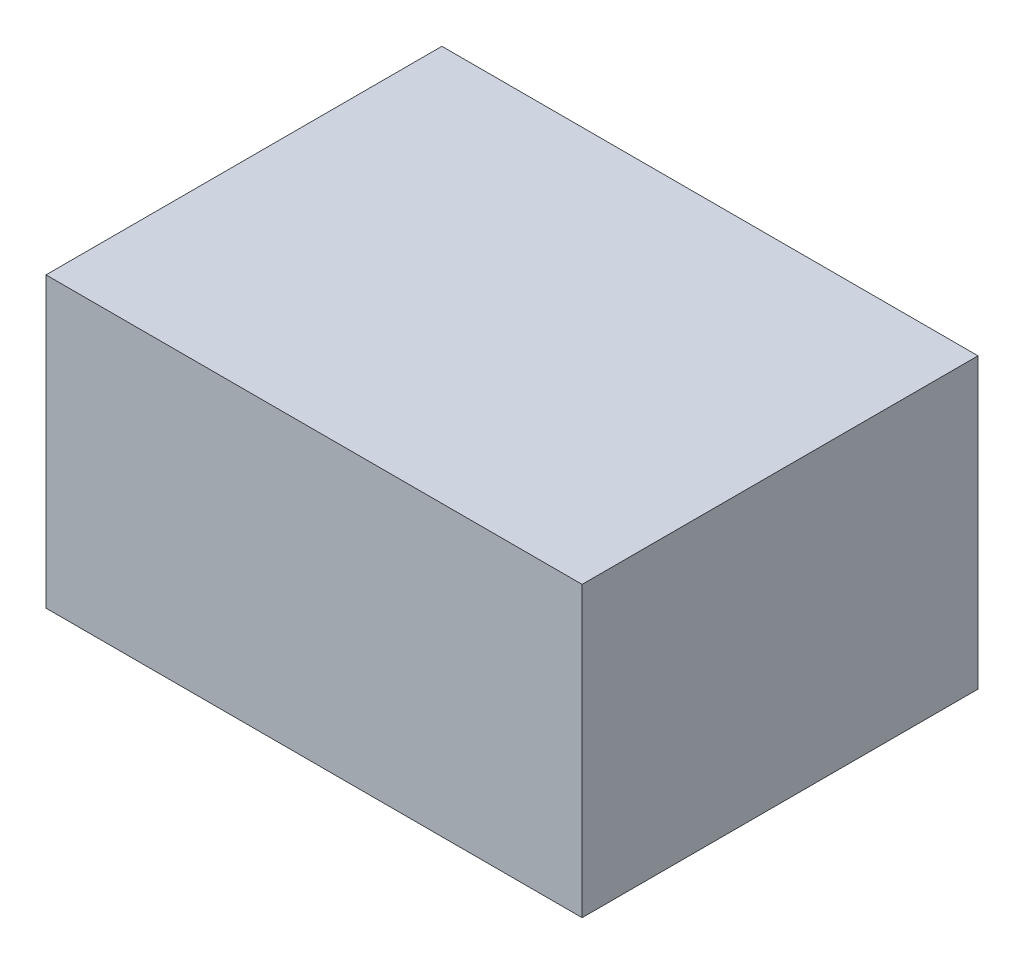
SolidWorks part; units mm, degrees
ref_plane "Ebene vorne" through (0, 0, 0) normal (0, 0, 1) x (1, 0, 0)
ref_plane "Ebene oben" through (0, 0, 0) normal (0, 1, 0) x (1, 0, 0)
ref_plane "Ebene rechts" through (0, 0, 0) normal (1, 0, 0) x (0, 0, -1)
sketch "Skizze1" plane through (0, 0, 0) normal (0, 0, 1) x (1, 0, 0)
  line L1 (325, 175) -> (-325, 175)
  line L2 (325, 175) -> (325, -175)
  line L3 (325, -175) -> (-325, -175)
  line L4 (-325, 175) -> (-325, -175)
  line L5 (325, 175) -> (-325, -175) construction
  line L6 (325, -175) -> (-325, 175) construction
  point P0 (0, 0)
  dimension "D1" = 350
  dimension "D2" = 650
extrude "Aufsatz-Linear austragen1" add sketch "Skizze1" along normal blind 480
